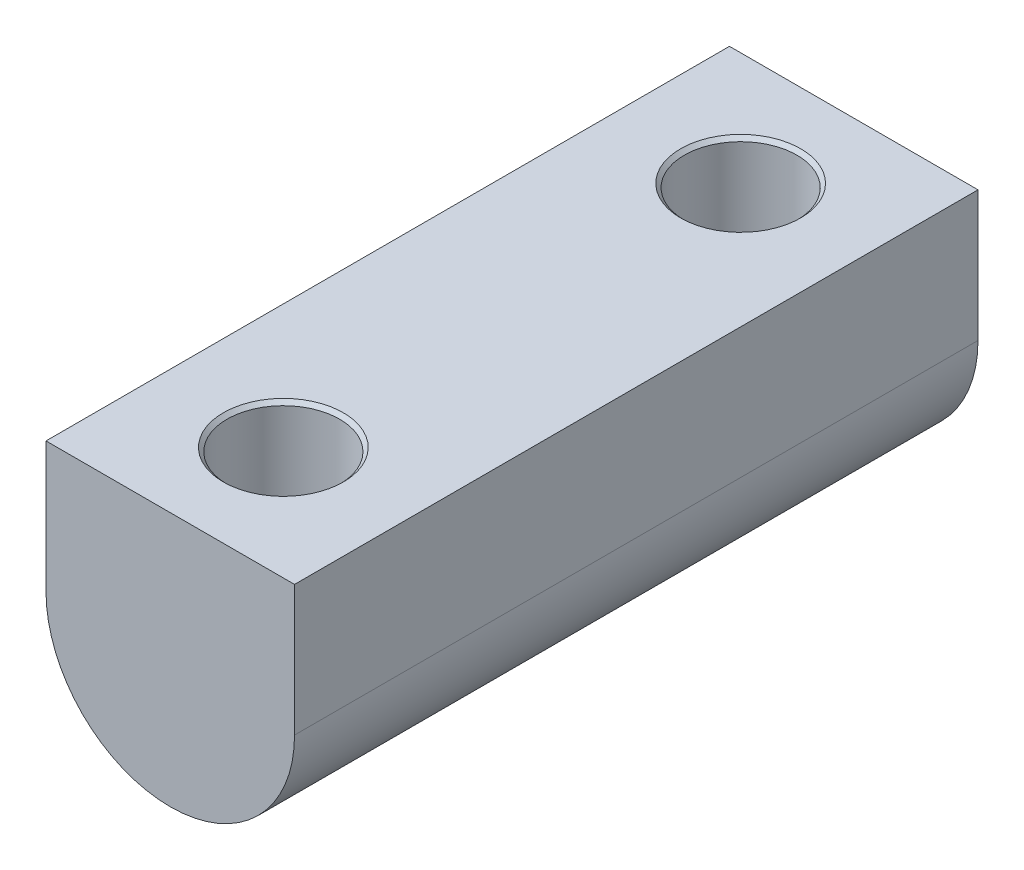
SolidWorks part; units mm, degrees
material "6061-T6 Al"
ref_plane "Front Plane" through (0, 0, 0) normal (0, 0, 1) x (1, 0, 0)
ref_plane "Top Plane" through (0, 0, 0) normal (0, 1, 0) x (1, 0, 0)
ref_plane "Right Plane" through (0, 0, 0) normal (1, 0, 0) x (0, 0, -1)
sketch "Sketch1" plane through (0, 0, 0) normal (0, 0, 1) x (1, 0, 0)
  line L0 (-25.4, 0) -> (-25.4, 26.67)
  line L1 (-25.4, 26.67) -> (25.4, 26.67)
  line L2 (25.4, 26.67) -> (25.4, 0)
  arc A0 (-25.4, 0) -> (25.4, 0) centre (0, 0) ccw
  dimension "D1" = 25.4
  dimension "D2" = 25.4
  dimension "D3" = 26.67
extrude "Extrude1" add sketch "Sketch1" along normal blind 139.7
hole_wizard "29/32 (0.90625) Diameter Hole1" positions "Sketch3" profile "Sketch2" hole size "29/32" standard "Ansi Inch" end condition through all
sketch "Sketch3" plane through (0, 26.67, 0) normal (0, 1, 0) x (-1, 0, 0)
  line L0 (0, 23.114) -> (0, 116.586) construction
  line L1 (25.4, 69.85) -> (0, 69.85) construction
  line L2 (25.4, 139.7) -> (25.4, 0) construction
  line L3 (0, 0) -> (0, 23.114) construction
  line L4 (-25.4, 0) -> (25.4, 0) construction
  point P0 (0, 23.114)
  point P1 (0, 116.586)
  dimension "D1" = 93.472
sketch "Sketch2" plane through (0, 26.67, 23.114) normal (1, 0, 0) x (0, 0, 1)
  line L0 (0, 0) -> (0, 52.07)
  line L1 (0, 52.07) -> (12.2682, 52.07)
  line L2 (11.5094, 51.3112) -> (11.5094, 0.7588)
  line L3 (11.5094, 0.7588) -> (12.2682, 0)
  line L5 (12.2682, 0) -> (0, 0)
  line L6 (-11.5094, 0.7588) -> (-12.2682, 0) construction
  line L7 (12.2682, 52.07) -> (11.5094, 51.3112)
  line L8 (-12.2682, 52.07) -> (-11.5094, 51.3112) construction
  line L11 (0, -6.35) -> (0, 107.95) construction
  dimension "Thru Hole Dia." = 23.0187
  dimension "Thru Hole Depth" = 52.07
  dimension "Near C'Sink Dia." = 24.5364
  dimension "Near C'Sink Angle" = 90
  dimension "Far C'Sink Dia." = 24.5364
  dimension "Far C'Sink Angle" = 90
